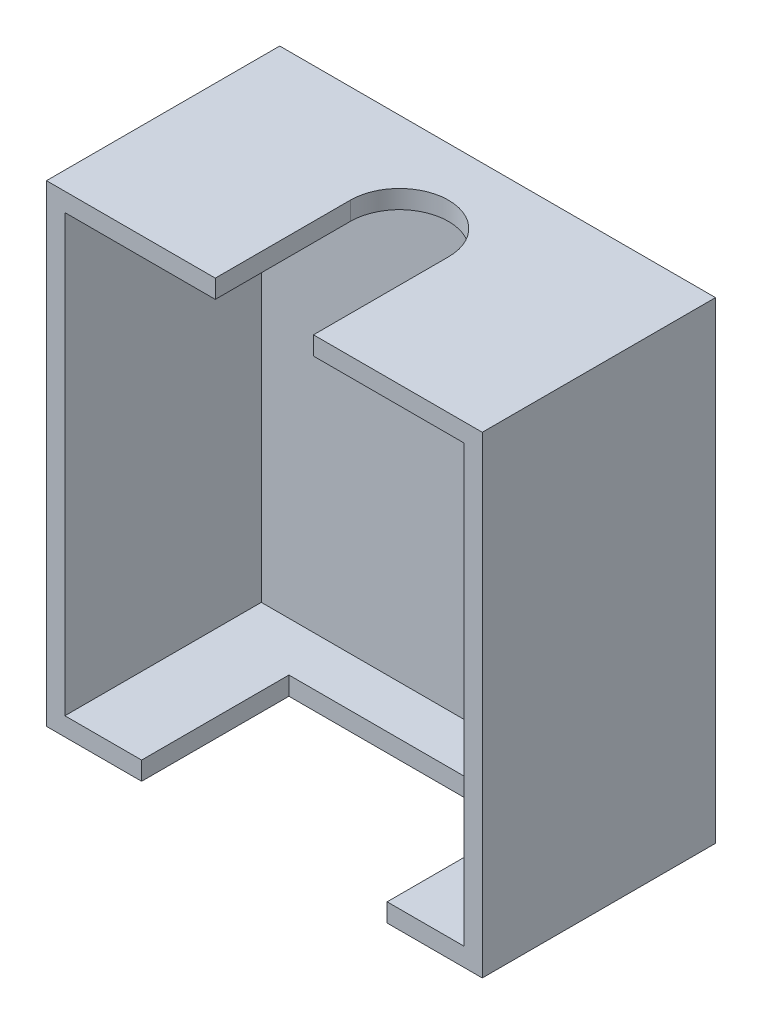
SolidWorks part; units mm, degrees
ref_plane "Plan de face" through (0, 0, 0) normal (0, 0, 1) x (1, 0, 0)
ref_plane "Plan de dessus" through (0, 0, 0) normal (0, 1, 0) x (1, 0, 0)
ref_plane "Plan de droite" through (0, 0, 0) normal (1, 0, 0) x (0, 0, -1)
sketch "Esquisse1" plane through (0, 0, 0) normal (0, 0, 1) x (1, 0, 0)
  line L1 (17.75, 19.25) -> (-17.75, 19.25)
  line L2 (17.75, 19.25) -> (17.75, -19.25)
  line L3 (17.75, -19.25) -> (-17.75, -19.25)
  line L4 (-17.75, 19.25) -> (-17.75, -19.25)
  line L5 (17.75, 19.25) -> (-17.75, -19.25) construction
  line L6 (17.75, -19.25) -> (-17.75, 19.25) construction
  point P0 (0, 0)
  dimension "D1" = 35.5
  dimension "D2" = 38.5
extrude "Boss.-Extru.1" add sketch "Esquisse1" along normal blind 19
sketch "Esquisse3" plane through (0, 0, 19) normal (0, 0, 1) x (1, 0, 0)
  line L1 (16.25, 17.75) -> (-16.25, 17.75)
  line L2 (16.25, 17.75) -> (16.25, -17.75)
  line L3 (16.25, -17.75) -> (-16.25, -17.75)
  line L4 (-16.25, 17.75) -> (-16.25, -17.75)
  line L5 (16.25, 17.75) -> (-16.25, -17.75) construction
  line L6 (16.25, -17.75) -> (-16.25, 17.75) construction
  point P0 (0, 0)
  dimension "D1" = 32.5
  dimension "D2" = 35.5
extrude "Enlèv. mat.-Extru.1" cut sketch "Esquisse3" against normal blind 16
sketch "Esquisse4" plane through (0, 19.25, 0) normal (0, 1, 0) x (1, 0, 0)
  line L0 (17.75, 0) -> (-17.75, 0) construction
  line L1 (-4, -8) -> (-4, -19)
  line L2 (17.75, -19) -> (-17.75, -19) construction
  line L3 (-4, -19) -> (4, -19)
  line L4 (4, -19) -> (4, -8)
  circle A0 centre (0, -8) radius 4
  line M4 (-17.75, -19) -> (17.75, -19)
  dimension "D1" = 8
  dimension "D2" = 8
extrude "Enlèv. mat.-Extru.2" cut sketch "Esquisse4" against normal blind 5 contours A0 L1 L4 M4 | A0
sketch "Esquisse5" plane through (0, -19.25, 0) normal (0, -1, 0) x (1, 0, 0)
  line L0 (-17.75, 19) -> (17.75, 19) construction
  line L1 (-10, 19) -> (10, 19)
  line L2 (-10, 19) -> (-10, 7)
  line L3 (-10, 7) -> (10, 7)
  line L4 (10, 19) -> (10, 7)
  line L5 (17.75, 19) -> (17.75, 0) construction
  dimension "D1" = 20
  dimension "D2" = 12
  dimension "D3" = 7.75
extrude "Enlèv. mat.-Extru.3" cut sketch "Esquisse5" against normal blind 5
